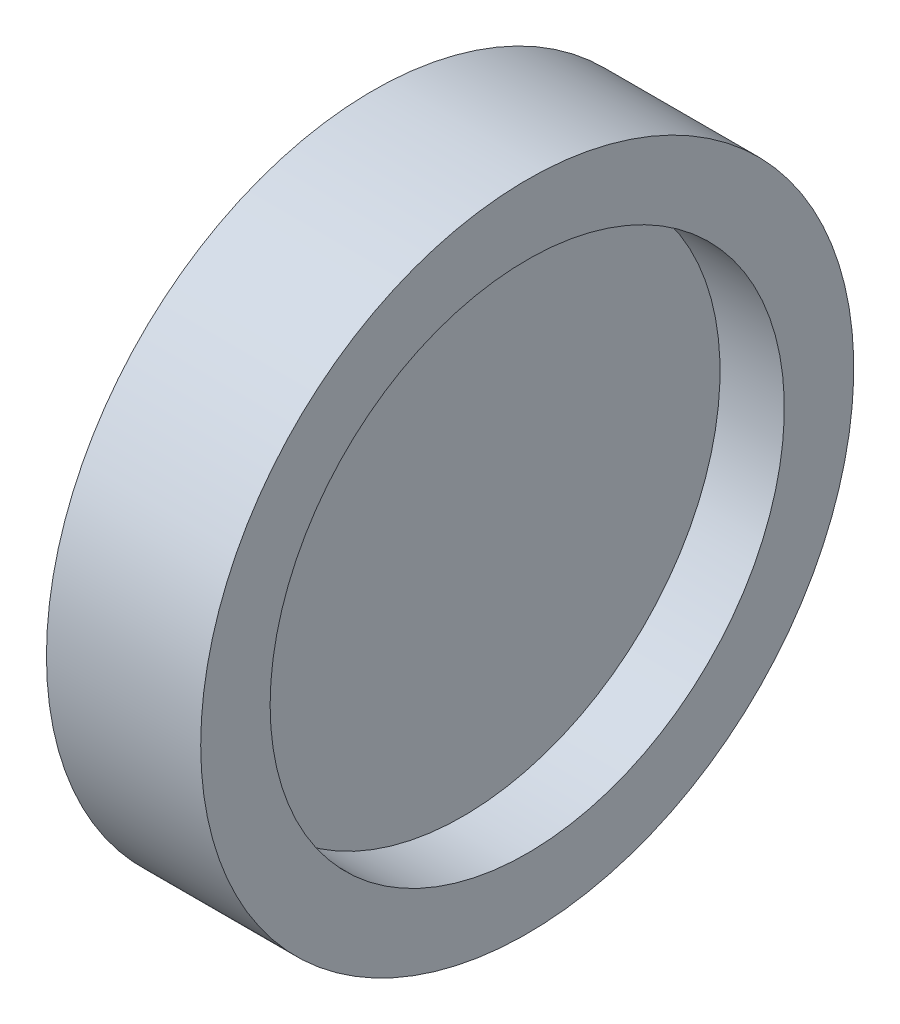
SolidWorks part; units mm, degrees
ref_plane "前视基准面" through (0, 0, 0) normal (0, 0, 1) x (1, 0, 0)
ref_plane "上视基准面" through (0, 0, 0) normal (0, 1, 0) x (1, 0, 0)
ref_plane "右视基准面" through (0, 0, 0) normal (1, 0, 0) x (0, 0, -1)
sketch "草图1" plane through (0, 0, 0) normal (0, 0, 1) x (1, 0, 0)
  line L0 (-0.5, 10) -> (-0.5, 0)
  line L2 (-0.5, 10) -> (0.5, 10)
  line L3 (-0.5, 0) -> (0.5, 0)
  line L4 (0.5, 10) -> (0.5, 0)
revolve "旋转2" add sketch "草图1" angle 360 about L3
sketch "草图4" plane through (0, 0, 0) normal (0, 0, 1) x (1, 0, 0)
  line L0 (-3, 12.7) -> (3, 12.7)
  line L1 (3, 12.7) -> (3, 10)
  line L2 (3, 10) -> (-3, 10)
  line L3 (0.5, 10) -> (-0.5, 10) construction
  line L4 (-3, 10) -> (-3, 12.7)
  line L5 (0, 10) -> (0, 12.7) construction
  line L6 (-1.6142, 0) -> (1.5903, 0) construction
revolve "旋转3" add sketch "草图4" angle 360 about L6
equation "\"D1@草图4\"=\"D1@草图1\""
